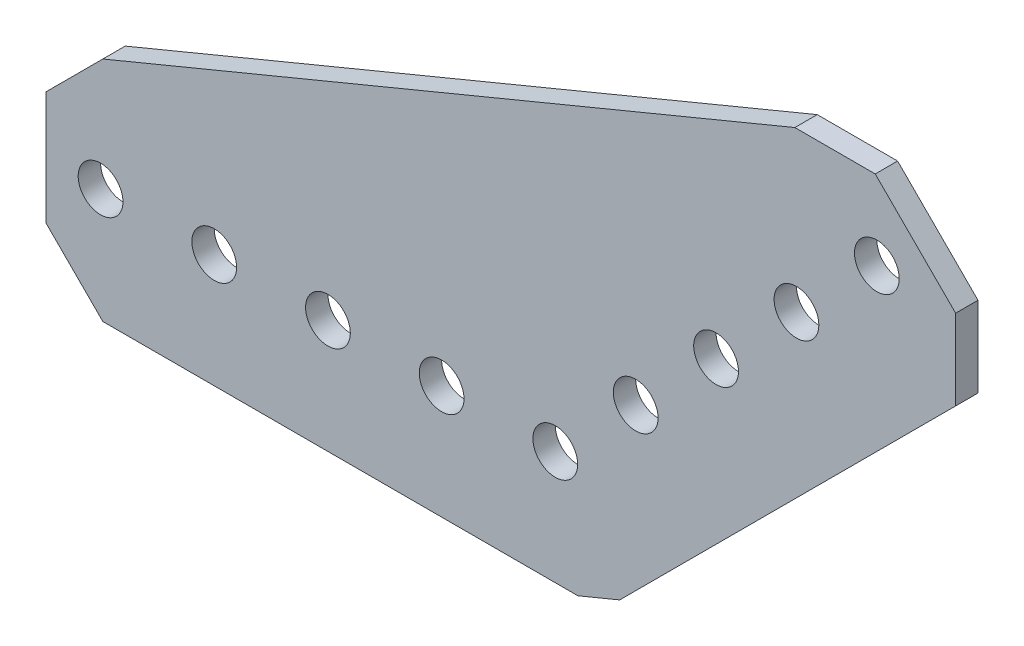
SolidWorks part; units mm, degrees
material "5052-H32"
ref_plane "Front Plane" through (0, 0, 0) normal (0, 0, 1) x (1, 0, 0)
ref_plane "Top Plane" through (0, 0, 0) normal (0, 1, 0) x (1, 0, 0)
ref_plane "Right Plane" through (0, 0, 0) normal (1, 0, 0) x (0, 0, -1)
ref_plane "Plane1" through (0, 0, -1.25) normal (0, 0, -1) x (-1, 0, 0)
sketch "Sketch1" plane through (0, 0, -1.25) normal (0, 0, -1) x (-1, 0, 0)
  line L0 (50.546, 12.7) -> (-26.7612, 44.7217)
  line L1 (-26.7612, 44.7217) -> (-35.7414, 44.7217)
  line L2 (-35.7414, 44.7217) -> (-44.7217, 35.7414)
  line L3 (-44.7217, 35.7414) -> (-44.7217, 26.7612)
  line L4 (-44.7217, 26.7612) -> (-7.194, -10.7665)
  line L5 (-7.194, -10.7665) -> (-2.5262, -12.7)
  line L6 (-2.5262, -12.7) -> (50.546, -12.7)
  line L7 (50.546, -12.7) -> (56.896, -6.35)
  line L8 (56.896, -6.35) -> (56.896, 6.35)
  line L9 (56.896, 6.35) -> (50.546, 12.7)
  circle A0 centre (12.7, 0) radius 2.5
  circle A1 centre (25.4, 0) radius 2.5
  circle A2 centre (0, 0) radius 2.5
  circle A3 centre (50.8, 0) radius 2.5
  circle A4 centre (38.1, 0) radius 2.5
  circle A5 centre (-35.921, 35.921) radius 2.5
  circle A6 centre (-26.9408, 26.9408) radius 2.5
  circle A7 centre (-17.9605, 17.9605) radius 2.5
  circle A8 centre (-8.9803, 8.9803) radius 2.5
extrude "Boss-Extrude1" add sketch "Sketch1" against normal blind 2.5
